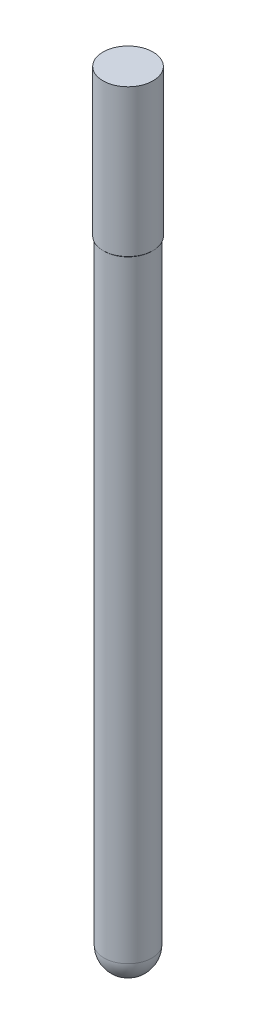
SolidWorks part; units mm, degrees
ref_plane "Plan de face" through (0, 0, 0) normal (0, 0, 1) x (1, 0, 0)
ref_plane "Plan de dessus" through (0, 0, 0) normal (0, 1, 0) x (1, 0, 0)
ref_plane "Plan de droite" through (0, 0, 0) normal (1, 0, 0) x (0, 0, -1)
sketch "Sketch1" plane through (0, 0, 0) normal (0, 0, 1) x (1, 0, 0)
  line L0 (0, 0) -> (0, 80)
  line L1 (0, 80) -> (2.5, 80)
  line L2 (2.45, 64.9) -> (2.45, 2.45)
  line L3 (2.5, 80) -> (2.55, 80)
  line L4 (2.55, 80) -> (2.55, 65)
  line L6 (2.55, 65) -> (2.45, 64.9)
  arc A0 (0, 0) -> (2.45, 2.45) centre (0, 2.45) ccw
  dimension "D1" = 2.5
  dimension "D2" = 80
  dimension "D3" = 15
  dimension "D4" = 0.05
  dimension "D5" = 0.1
revolve "Revolve1" add sketch "Sketch1" angle 360 about L0
